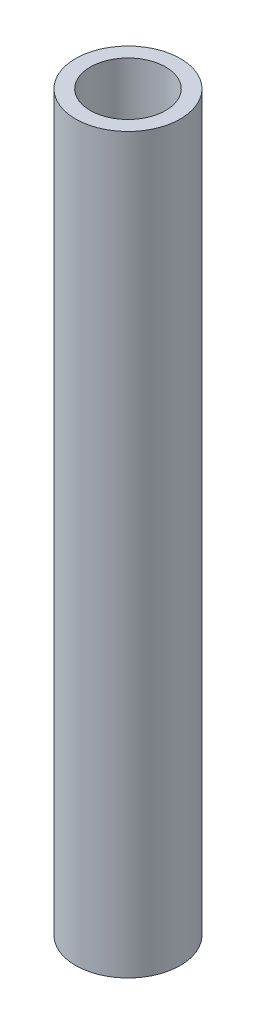
SolidWorks part; units mm, degrees
material "AISI 316 Stainless Steel Sheet (SS)"
ref_plane "Front Plane" through (0, 0, 0) normal (0, 0, 1) x (1, 0, 0)
ref_plane "Top Plane" through (0, 0, 0) normal (0, 1, 0) x (1, 0, 0)
ref_plane "Right Plane" through (0, 0, 0) normal (1, 0, 0) x (0, 0, -1)
sketch "Sketch1" plane through (0, 0, 0) normal (0, 1, 0) x (1, 0, 0)
  circle A0 centre (0, 0) radius 3.175
  circle A1 centre (0, 0) radius 2.286
  dimension "D1" = 6.35
  dimension "D2" = 4.572
extrude "Boss-Extrude1" add sketch "Sketch1" along normal blind 44.45
